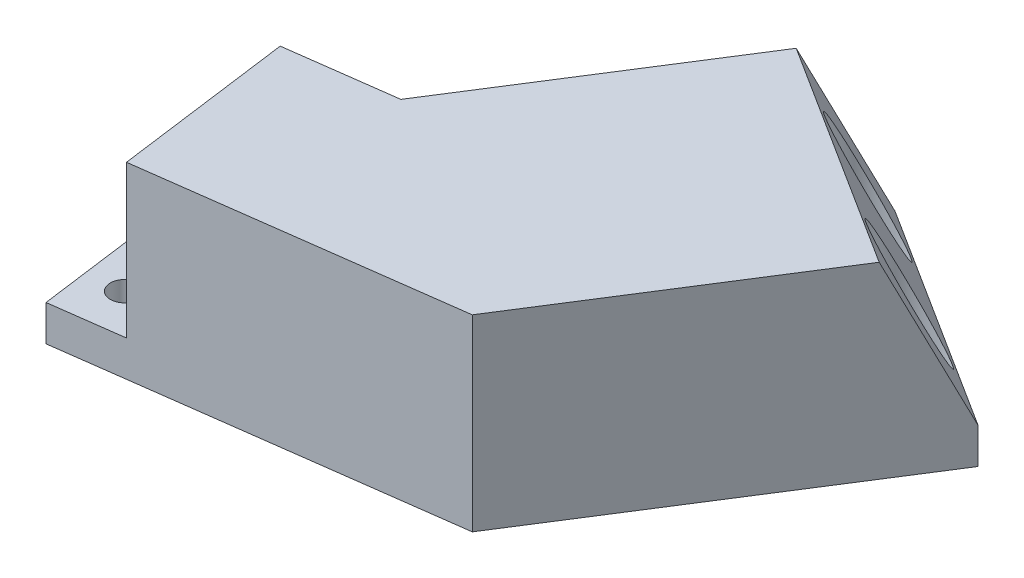
SolidWorks part; units mm, degrees
ref_plane "Спереди" through (0, 0, 0) normal (0, 0, 1) x (1, 0, 0)
ref_plane "Сверху" through (0, 0, 0) normal (0, 1, 0) x (1, 0, 0)
ref_plane "Справа" through (0, 0, 0) normal (1, 0, 0) x (0, 0, -1)
sketch "Sketch1" plane through (0, 0, 0) normal (0, 1, 0) x (1, 0, 0)
  line L0 (0, 0) -> (-19.8234, -2.6518)
  line L1 (-19.8234, -2.6518) -> (-17.1716, -22.4752)
  line L2 (-17.1716, -22.4752) -> (24.8344, -16.856)
  line L3 (24.8344, -16.856) -> (46.7569, 17.7141)
  line L4 (46.7569, 17.7141) -> (21.4217, 33.7803)
  line L5 (21.4217, 33.7803) -> (0, 0)
  line L6 (0, 0) -> (2.6518, -19.8234) construction
  dimension "D1" = 130
  dimension "D2" = 20
  dimension "D3" = 20
  dimension "D4" = 30
  dimension "D5" = 90
  dimension "D6" = 40
extrude "Boss-Extrude1" add sketch "Sketch1" along normal blind 21
sketch "Sketch2" plane through (0, 21, 0) normal (0, 1, 0) x (1, 0, 0)
  line L0 (21.4217, 33.7803) -> (17.1373, 27.0243)
  line L1 (21.4217, 33.7803) -> (0, 0) construction
  line L2 (17.1373, 27.0243) -> (42.4726, 10.958)
  line L3 (24.8344, -16.856) -> (46.7569, 17.7141) construction
  line L4 (42.4726, 10.958) -> (46.7569, 17.7141)
  line L5 (46.7569, 17.7141) -> (21.4217, 33.7803)
  line L6 (-19.8234, -2.6518) -> (-17.1716, -22.4752)
  line L7 (-17.1716, -22.4752) -> (-9.2422, -21.4145)
  line L8 (-17.1716, -22.4752) -> (24.8344, -16.856) construction
  line L9 (-9.2422, -21.4145) -> (-11.8941, -1.5911)
  line L10 (0, 0) -> (-19.8234, -2.6518) construction
  line L11 (-11.8941, -1.5911) -> (-19.8234, -2.6518)
  dimension "D1" = 8
extrude "Cut-Extrude1" cut sketch "Sketch2" against normal offset from surface (17 mm away) 4 up to face at (9.3363, 0, -1.5852)
sketch "Sketch3" plane through (0, 21, 0) normal (0, 1, 0) x (1, 0, 0)
  line L0 (18.0642, 22.8841) -> (1.7843, -2.788)
  line L1 (1.7843, -2.788) -> (-8.5228, -4.1668)
  line L2 (-8.5228, -4.1668) -> (-6.6665, -18.0432)
  line L3 (-6.6665, -18.0432) -> (23.0501, -14.068)
  line L4 (23.0501, -14.068) -> (38.3324, 10.0311)
  line L5 (38.3324, 10.0311) -> (18.0642, 22.8841)
  line L6 (18.0642, 22.8841) -> (17.864, 23.073)
  line L7 (17.1373, 27.0243) -> (0, 0) construction
  line L9 (0, 0) -> (-11.8941, -1.5911) construction
  line L10 (-9.2422, -21.4145) -> (-11.8941, -1.5911) construction
  line L11 (-9.2422, -21.4145) -> (24.8344, -16.856) construction
  line L12 (24.8344, -16.856) -> (42.4726, 10.958) construction
  line L13 (17.1373, 27.0243) -> (42.4726, 10.958) construction
  dimension "D1" = 3
  dimension "D2" = 3
  dimension "D3" = 3
  dimension "D4" = 3
  dimension "D5" = 3
  dimension "D6" = 3
extrude "Cut-Extrude2" cut sketch "Sketch3" against normal through all from offset 3 contours L4 L5 L0 L1 L2 L3 offset against normal yes
sketch "Sketch4" plane through (2.5335, 0, 1.6066) normal (0.8445, 0, 0.5355) x (0.5355, 0, -0.8445)
  line L0 (13.8005, 0) -> (13.8005, 18) construction
  line L1 (29, 0) -> (-1.3989, 0) construction
  line L2 (29, 18) -> (-1.3989, 18) construction
  line L4 (3.3005, 1) -> (24.3005, 1) construction
  line L5 (3.3005, 1) -> (3.3005, 17) construction
  line L6 (3.3005, 17) -> (24.3005, 17) construction
  line L7 (24.3005, 1) -> (24.3005, 17) construction
  line L8 (3.3005, 1) -> (24.3005, 17) construction
  line L9 (3.3005, 17) -> (24.3005, 1) construction
  circle A0 centre (13.8005, 9) radius 4.5
  dimension "D1" = 9
  dimension "D2" = 16
  dimension "D3" = 21
extrude "Cut-Extrude3" cut sketch "Sketch4" against normal through all
sketch "Sketch5" plane through (0, 4, 0) normal (0, 1, 0) x (1, 0, 0)
  line L0 (19.2795, 30.4023) -> (44.6148, 14.3361) construction
  line L1 (21.4217, 33.7803) -> (17.1373, 27.0243) construction
  line L2 (42.4726, 10.958) -> (46.7569, 17.7141) construction
  line L3 (-15.8587, -2.1215) -> (-13.2069, -21.9449) construction
  line L4 (-11.8941, -1.5911) -> (-19.8234, -2.6518) construction
  line L5 (-17.1716, -22.4752) -> (-9.2422, -21.4145) construction
  circle A0 centre (26.0356, 26.118) radius 1.6
  circle A1 centre (38.7032, 18.0848) radius 1.6
  circle A2 centre (-15.1958, -7.0773) radius 1.6
  circle A3 centre (-13.8699, -16.989) radius 1.6
  point P20 (-14.5328, -12.0332)
  dimension "D1" = 3.2
  dimension "D2" = 10
  dimension "D3" = 5
  dimension "D4" = 15
  dimension "D5" = 8
extrude "Cut-Extrude4" cut sketch "Sketch5" against normal through all
sketch "Sketch6" plane through (0, 0, 0) normal (-0.8445, 0, -0.5355) x (-0.5355, 0, 0.8445)
  line L0 (-24, 0) -> (-24, 21) construction
  line L1 (-40, 0) -> (0, 0) construction
  line L2 (-32, 21) -> (0, 21) construction
  line L3 (-32, 4) -> (-32, 21) construction
  text T0 "<b>    ALT</b>" font "Arial" height 3
  dimension "D1" = 8
extrude "Cut-Extrude5" cut sketch "Sketch6" against normal blind 0.5
sketch "Sketch8" plane through (0, 0, 0) normal (-0.8445, 0, -0.5355) x (-0.5355, 0, 0.8445)
  line L0 (-40, 4) -> (-32, 21)
  line L1 (-32, 21) -> (-32, 4)
  line L2 (-32, 4) -> (-40, 4)
extrude "Boss-Extrude2" add sketch "Sketch8" against normal up to surface (30 mm away) up to face at (38.0213, 8.3333, -3.9387)
sketch "Sketch10" plane through (0, 0, 0) normal (0, -1, 0) x (1, 0, 0)
  circle A0 centre (26.0356, -26.118) radius 1.6
  circle A1 centre (38.7032, -18.0848) radius 1.6
  circle A2 centre (-15.1958, 7.0773) radius 1.6
  circle A3 centre (-13.8699, 16.989) radius 1.6
  circle A4 centre (38.7032, -18.0848) radius 1.6 construction
extrude "Cut-Extrude6" cut sketch "Sketch10" against normal through all
sketch "Sketch11" plane through (0, 0, 0) normal (0, -1, 0) x (1, 0, 0)
  circle A0 centre (-15.1958, 7.0773) radius 3.5
  circle A1 centre (-13.8699, 16.989) radius 3.5
  circle A2 centre (38.7032, -18.0848) radius 3.5
  circle A3 centre (26.0356, -26.118) radius 3.5
  dimension "D1" = 7
extrude "Cut-Extrude7" cut sketch "Sketch11" against normal through all from offset 4 offset against normal yes
sketch "Sketch12" plane through (-8.9205, 0, 1.1933) normal (0.9912, 0, -0.1326) x (-0.1326, 0, -0.9912)
  line L0 (-10, 0) -> (-10, 18) construction
  line L1 (-3, 0) -> (-17, 0) construction
  line L2 (-3, 18) -> (-17, 18) construction
  circle A0 centre (-10, 11) radius 3
  dimension "D1" = 6
  dimension "D2" = 11
extrude "Cut-Extrude8" cut sketch "Sketch12" against normal through all
sketch "Sketch13" plane through (0, 0, 0) normal (-0.1326, 0, -0.9912) x (-0.9912, 0, 0.1326)
  line L0 (7, 0) -> (7, 21) construction
  line L1 (0, 0) -> (20, 0) construction
  line L2 (0, 21) -> (12, 21) construction
  line L3 (12, 4) -> (12, 21) construction
  text T0 "<b>     R / B</b>" font "Arial" height 3
  dimension "D1" = 5
extrude "Cut-Extrude9" cut sketch "Sketch13" against normal blind 0.5
